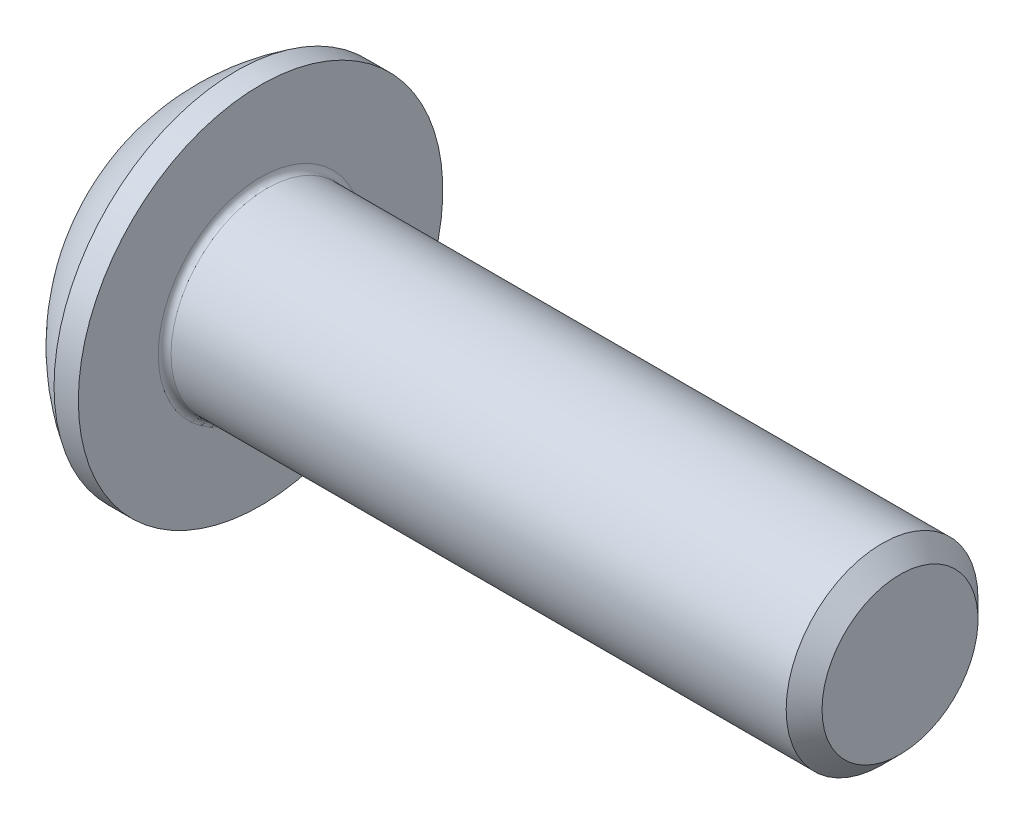
SolidWorks part; units mm, degrees
ref_plane "Plane1" through (0, 0, 0) normal (0, 0, 1) x (1, 0, 0)
ref_plane "Plane2" through (0, 0, 0) normal (0, 1, 0) x (1, 0, 0)
ref_plane "Plane3" through (0, 0, 0) normal (1, 0, 0) x (0, 0, -1)
sketch "BodySke" plane through (0, 0, 0) normal (0, 0, 1) x (1, 0, 0)
  line L0 (11.65, 0) -> (11.65, 1.2195)
  line L1 (11.3695, 1.5) -> (1.65, 1.5)
  line L2 (1.65, 1.5) -> (1.65, 2.85)
  line L3 (1.65, 2.85) -> (1.27, 2.85)
  line L4 (0, 0) -> (101.6, 0) construction
  line L5 (1.65, -2.85) -> (1.27, -2.85) construction
  line L6 (55.6768, -1.5) -> (1.65, -1.5) construction
  line L7 (11.65, 0) -> (0, 0)
  line L8 (0, 1.425) -> (0, -1.425) construction
  line L9 (0, 0) -> (0, 1.425)
  line L10 (11.65, 1.2195) -> (11.3695, 1.5)
  line L11 (11.65, -1.2195) -> (11.3695, -1.5) construction
  line L12 (2.15, 9.525) -> (2.15, -1.5) construction
  line L13 (1.65, 9.525) -> (1.65, -1.5) construction
  arc A1 (0, 1.425) -> (1.27, 2.85) centre (3.0334, 0) cw
  dimension "Diameter" = 3
  dimension "Length" = 10
  dimension "Head_dia" = 5.7
  dimension "D1" = 2.85
  dimension "Head_ht" = 1.65
  dimension "Head_side_ht" = 0.38
  dimension "Minor_dia" = 2.439
  dimension "Body_ch_ang" = 45
  dimension "Advance" = 0.5
  dimension "Thread_nom" = 10
revolve "BaseBody" add sketch "BodySke" angle 360 about L4
cosmetic thread "ThreadCosmetic" [suppressed] parameters "Thread_length"=9, "Thread_minor"=2.439
fillet "Fillet1" radius 0.1 1 edges at (1.65, 0, 1.5)
sketch "Sketch2" plane through (0, 0, 0) normal (0, 0, 1) x (1, 0, 0)
  line L0 (0, 1) -> (1.04, 1)
  line L1 (1.04, 1) -> (1.6174, 0)
  line L3 (1.6174, 0) -> (0, 0)
  line L4 (0, 0) -> (0, 1)
  line L5 (0, -1) -> (1.04, -1) construction
  line L6 (0, 0) -> (47.625, 0) construction
  dimension "D2" = 60
  dimension "PreBroach_depth" = 1.04
  dimension "PreBroach_dia" = 2
revolve "PreBroach" cut sketch "Sketch2" angle 360 about L6
sketch "Sketch3" plane through (0, 0, 0) normal (1, 0, 0) x (0, 0, -1)
  line L0 (-1, -0.5774) -> (-1, 0.5774)
  line L1 (-1, 0.5774) -> (0, 1.1547)
  line L2 (0, 1.1547) -> (1, 0.5774)
  line L3 (1, 0.5774) -> (1, -0.5774)
  line L4 (1, -0.5774) -> (0, -1.1547)
  line L5 (0, -1.1547) -> (-1, -0.5774)
  dimension "Hex_size" = 2
  dimension "D3" = 2
  dimension "D1" = 1
  dimension "D2" = 1
extrude "Hex" cut sketch "Sketch3" along normal blind 1.04
sketch "ThdSchSke" plane through (0, 0, 0) normal (0, 0, 1) x (1, 0, 0)
  line L0 (2.65, -1.2195) -> (2.4536, -1.5)
  line L1 (2.65, -1.2195) -> (2.8464, -1.5)
  line L2 (2.8464, -1.5) -> (2.8464, -1.875)
  line L3 (-3.175, 0) -> (5.1513, 0) construction
  line L5 (2.8464, -1.875) -> (2.4536, -1.875)
  line L6 (2.4536, -1.875) -> (2.4536, -1.5)
  dimension "Diameter" = 3
  dimension "Thread_minor" = 2.439
  dimension "SideAngle" = 55
  dimension "VeeAngle" = 70
  dimension "Overcut" = 3.75
  dimension "Start" = 2.65
revolve "ThreadSchematic" [suppressed] cut sketch "ThdSchSke" angle 360 about L3
pattern_linear "ThdSchPat" [suppressed]
equation "\"D1@BodySke\" = \"Head_dia@BodySke\" * .5"
equation "\"Thread_minor@ThreadCosmetic\" = \"Minor_dia@BodySke\""
equation "\"D1@Sketch3\" = \"Hex_size@Sketch3\" / 2"
equation "\"D2@Sketch3\" = \"D1@Sketch3\""
equation "\"D3@Sketch3\" = \"Hex_size@Sketch3\""
equation "\"Thread_length@ThreadCosmetic\" = ((sgn( (\"Length@BodySke\" - \"Advance@BodySke\" * 2.0) - \"Thread_nom@BodySke\" )-1)*( (\"Length@BodySke\" - \"Advance@BodySke\" * 2.0) - \"Thread_nom@BodySke\" ))/-2+ \"Thread_nom@BodySke\""
equation "\"Thread_minor@ThdSchSke\" = \"Minor_dia@BodySke\""
equation "\"Diameter@ThdSchSke\" = \"Diameter@BodySke\""
equation "\"Overcut@ThdSchSke\" = \"Diameter@BodySke\" * 1.25"
equation "\"Start@ThdSchSke\" = \"Head_ht@BodySke\" + \"Length@BodySke\" - \"Thread_length@ThreadCosmetic\"  '---Non-countersunk---"
equation "\"Num_threads@ThdSchPat\" = int( \"Thread_length@ThreadCosmetic\" / \"Advance@BodySke\" + 0.999 )  + 1"
equation "\"Advance@ThdSchPat\" = \"Thread_length@ThreadCosmetic\" /  (\"Num_threads@ThdSchPat\" - 1) 'relax it"
equation "\"Num_threads@ThdSchPat\" = \"Num_threads@ThdSchPat\" - sgn( \"Num_threads@ThdSchPat\" - 1) '---chamfered tips only---"
